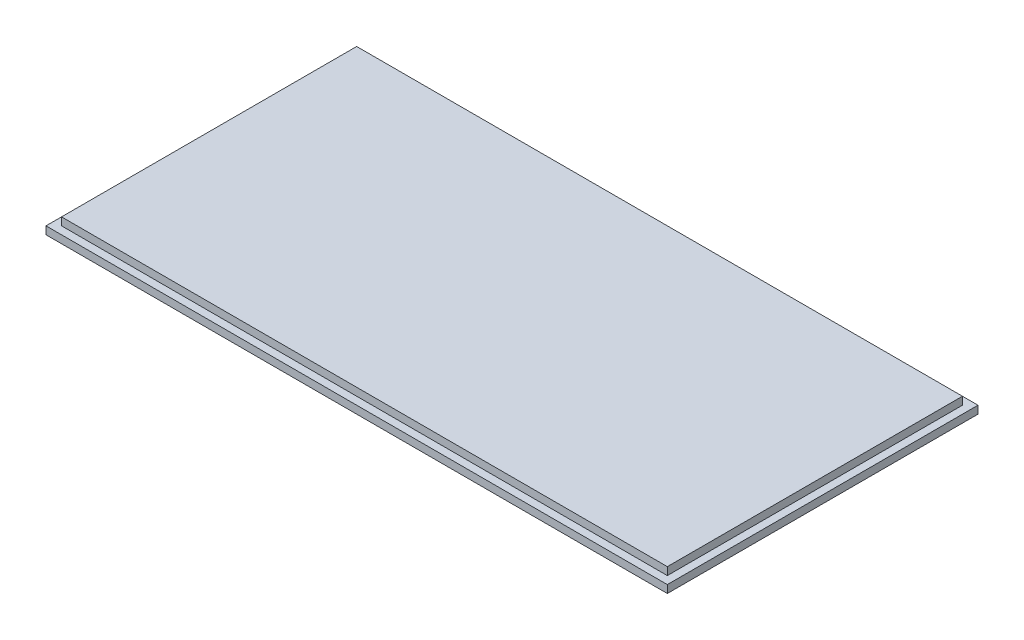
SolidWorks part; units mm, degrees
ref_plane "Front Plane" through (0, 0, 0) normal (0, 0, 1) x (1, 0, 0)
ref_plane "Top Plane" through (0, 0, 0) normal (0, 1, 0) x (1, 0, 0)
ref_plane "Right Plane" through (0, 0, 0) normal (1, 0, 0) x (0, 0, -1)
sketch "Sketch1" plane through (0, 0, 0) normal (0, 1, 0) x (1, 0, 0)
  line L1 (-60, 30) -> (60, 30)
  line L2 (-60, 30) -> (-60, -30)
  line L3 (-60, -30) -> (60, -30)
  line L4 (60, 30) -> (60, -30)
  line L5 (-60, 30) -> (60, -30) construction
  line L6 (-60, -30) -> (60, 30) construction
  point P0 (0, 0)
  dimension "D1" = 120
  dimension "D2" = 60
extrude "Boss-Extrude1" add sketch "Sketch1" along normal blind 3
sketch "Sketch2" plane through (0, 3, 0) normal (0, 1, 0) x (1, 0, 0)
  line L0 (60, 30) -> (-60, 30) construction
  line L1 (-58.5, 28.5) -> (58.5, 28.5)
  line L2 (-58.5, 28.5) -> (-58.5, -28.5)
  line L3 (-58.5, -28.5) -> (58.5, -28.5)
  line L4 (58.5, 28.5) -> (58.5, -28.5)
  line L5 (-58.5, 28.5) -> (58.5, -28.5) construction
  line L6 (-58.5, -28.5) -> (58.5, 28.5) construction
  line L7 (-60, 30) -> (-60, -30) construction
  point P0 (0, 0)
  dimension "D1" = 1.5
  dimension "D2" = 1.5
extrude "Cut-Extrude1" cut sketch "Sketch2" against normal blind 1.5 flip side to cut
